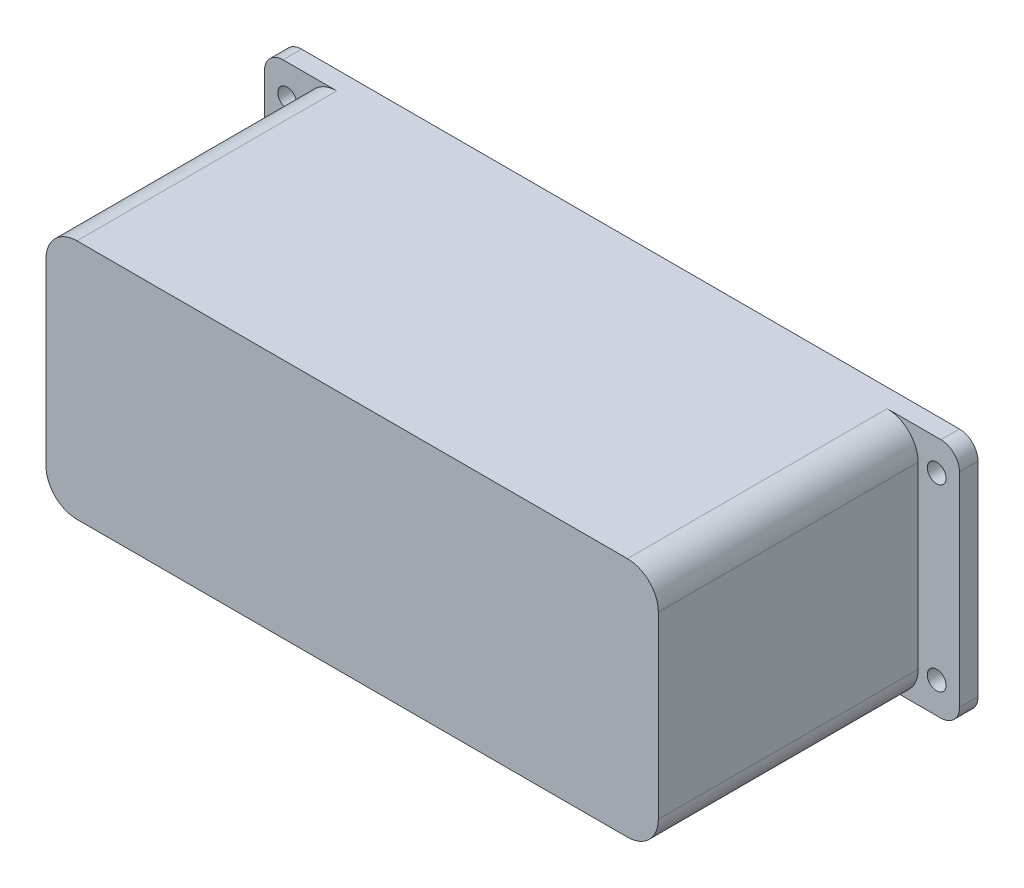
SolidWorks part; units mm, degrees
material "ABS"
ref_plane "前视基准面" through (0, 0, 0) normal (0, 0, 1) x (1, 0, 0)
ref_plane "上视基准面" through (0, 0, 0) normal (0, 1, 0) x (1, 0, 0)
ref_plane "右视基准面" through (0, 0, 0) normal (1, 0, 0) x (0, 0, -1)
other "Configuration Table"
sketch "草图1" plane through (0, 0, 0) normal (0, 0, 1) x (1, 0, 0)
  line L1 (-79.5, -19.5) -> (79.5, -19.5)
  line L2 (-79.5, -19.5) -> (-79.5, 19.5)
  line L3 (-79.5, 19.5) -> (79.5, 19.5)
  line L4 (79.5, -19.5) -> (79.5, 19.5)
  line L5 (-79.5, -19.5) -> (79.5, 19.5) construction
  line L6 (-79.5, 19.5) -> (79.5, -19.5) construction
  point P0 (0, 0)
  dimension "D1" = 159
  dimension "D2" = 39
extrude "凸台-拉伸1" add sketch "草图1" along normal blind 2
fillet "圆角1" radius 3 4 edges at (-79.5, -19.5, 1) (-79.5, 19.5, 1) (79.5, -19.5, 1) (79.5, 19.5, 1)
sketch "草图2" plane through (0, 0, 2) normal (0, 0, 1) x (1, 0, 0)
  line L0 (79.5, -16.5) -> (79.5, 16.5) construction
  line L1 (73, -7.5) -> (86, -7.5)
  line L2 (73, -7.5) -> (73, 7.5)
  line L3 (73, 7.5) -> (86, 7.5)
  line L4 (86, -7.5) -> (86, 7.5)
  line L5 (73, -7.5) -> (86, 7.5) construction
  line L6 (73, 7.5) -> (86, -7.5) construction
  line L8 (-52.5, -14.5) -> (52.5, -14.5) construction
  line L9 (-52.5, -14.5) -> (-52.5, 14.5) construction
  line L10 (-52.5, 14.5) -> (52.5, 14.5) construction
  line L11 (52.5, -14.5) -> (52.5, 14.5) construction
  line L12 (-52.5, -14.5) -> (52.5, 14.5) construction
  line L13 (-52.5, 14.5) -> (52.5, -14.5) construction
  circle A0 centre (52.5, 14.5) radius 1.52
  circle A1 centre (-52.5, 14.5) radius 1.52
  circle A2 centre (-52.5, -14.5) radius 1.52
  circle A3 centre (52.5, -14.5) radius 1.52
  point P0 (79.5, 0)
  point P7 (0, 0)
  dimension "D5" = 3.04
  dimension "D1" = 105
  dimension "D2" = 29
  dimension "D3" = 13
  dimension "D4" = 15
extrude "切除-拉伸1" cut sketch "草图2" against normal blind 55
ref_plane "基准面1" through (0, 0, 4) normal (0, 0, 1) x (1, 0, 0)
sketch "草图4" plane through (0, 0, 4) normal (0, 0, 1) x (1, 0, 0)
  line L8 (79.5, -16.5) -> (79.5, -7.5)
  line L9 (79.5, -7.5) -> (73, -7.5)
  line L10 (73, -7.5) -> (73, 7.5)
  line L11 (73, 7.5) -> (79.5, 7.5)
  line L12 (79.5, 7.5) -> (79.5, 16.5)
  line L13 (76.5, 19.5) -> (-76.5, 19.5)
  line L14 (-79.5, 16.5) -> (-79.5, -16.5)
  line L15 (-76.5, -19.5) -> (76.5, -19.5)
  line L16 (79.5, -16.5) -> (79.5, -7.5)
  line L17 (79.5, -7.5) -> (73, -7.5)
  line L18 (73, -7.5) -> (73, 7.5)
  line L19 (73, 7.5) -> (79.5, 7.5)
  line L20 (79.5, 7.5) -> (79.5, 16.5)
  line L21 (76.5, 19.5) -> (-76.5, 19.5)
  line L22 (-79.5, 16.5) -> (-79.5, -16.5)
  line L23 (-76.5, -19.5) -> (76.5, -19.5)
  arc A4 (79.5, 16.5) -> (76.5, 19.5) centre (76.5, 16.5) ccw
  arc A5 (-76.5, 19.5) -> (-79.5, 16.5) centre (-76.5, 16.5) ccw
  arc A6 (-79.5, -16.5) -> (-76.5, -19.5) centre (-76.5, -16.5) ccw
  arc A7 (76.5, -19.5) -> (79.5, -16.5) centre (76.5, -16.5) ccw
  arc A8 (79.5, 16.5) -> (76.5, 19.5) centre (76.5, 16.5) ccw
  arc A9 (-76.5, 19.5) -> (-79.5, 16.5) centre (-76.5, 16.5) ccw
  arc A10 (-79.5, -16.5) -> (-76.5, -19.5) centre (-76.5, -16.5) ccw
  arc A11 (76.5, -19.5) -> (79.5, -16.5) centre (76.5, -16.5) ccw
  dimension "D1" = 0
extrude "凸台-拉伸2" add sketch "草图4" along normal blind 3 separate body
sketch "草图5" plane through (0, 0, 7) normal (0, 0, 1) x (1, 0, 0)
  line L0 (76.5, 19.5) -> (-76.5, 19.5) construction
  line L1 (-49.5, -19.5) -> (49.5, -19.5)
  line L2 (-49.5, -19.5) -> (-49.5, 19.5)
  line L3 (-49.5, 19.5) -> (49.5, 19.5)
  line L4 (49.5, -19.5) -> (49.5, 19.5)
  line L5 (-49.5, -19.5) -> (49.5, 19.5) construction
  line L6 (-49.5, 19.5) -> (49.5, -19.5) construction
  circle A0 centre (52.5, 14.5) radius 1.52 construction
  point P0 (0, 0)
  dimension "D1" = 3
extrude "凸台-拉伸3" add sketch "草图5" along normal blind 44
sketch "草图7" plane through (0, 0, 7) normal (0, 0, 1) x (1, 0, 0)
  circle A0 centre (-52.5, -14.5) radius 1.52 construction
  circle A1 centre (-52.5, 14.5) radius 1.52 construction
  circle A2 centre (52.5, -14.5) radius 1.52 construction
  circle A3 centre (52.5, 14.5) radius 1.52 construction
  circle A4 centre (-52.5, -14.5) radius 1.52
  circle A5 centre (-52.5, 14.5) radius 1.52
  circle A6 centre (52.5, -14.5) radius 1.52
  circle A7 centre (52.5, 14.5) radius 1.52
extrude "切除-拉伸2" cut sketch "草图7" against normal blind 45
fillet "圆角2" radius 5 4 edges at (49.5, 19.5, 29) (-49.5, 19.5, 29) (-49.5, -19.5, 29) (49.5, -19.5, 29)
sketch "草图8" plane through (0, 0, 4) normal (0, 0, -1) x (-1, 0, 0)
  line L8 (-48.18, 14.5) -> (-48.18, -14.5)
  line L9 (44.5, 18.18) -> (-44.5, 18.18)
  line L10 (48.18, -14.5) -> (48.18, 14.5)
  line L11 (-44.5, -18.18) -> (44.5, -18.18)
  line L12 (-48.18, 14.5) -> (-48.18, -14.5)
  line L13 (44.5, 18.18) -> (-44.5, 18.18)
  line L14 (48.18, -14.5) -> (48.18, 14.5)
  line L15 (-44.5, -18.18) -> (44.5, -18.18)
  arc A4 (48.18, 14.5) -> (44.5, 18.18) centre (44.5, 14.5) ccw
  arc A5 (48.18, 14.5) -> (44.5, 18.18) centre (44.5, 14.5) ccw
  arc A6 (44.5, -18.18) -> (48.18, -14.5) centre (44.5, -14.5) ccw
  arc A7 (44.5, -18.18) -> (48.18, -14.5) centre (44.5, -14.5) ccw
  arc A8 (-48.18, -14.5) -> (-44.5, -18.18) centre (-44.5, -14.5) ccw
  arc A9 (-48.18, -14.5) -> (-44.5, -18.18) centre (-44.5, -14.5) ccw
  arc A10 (-44.5, 18.18) -> (-48.18, 14.5) centre (-44.5, 14.5) ccw
  arc A11 (-44.5, 18.18) -> (-48.18, 14.5) centre (-44.5, 14.5) ccw
  dimension "D1" = 1.32
extrude "切除-拉伸4" cut sketch "草图8" against normal blind 43
sketch "草图9" plane through (0, 0, 0) normal (0, 0, -1) x (-1, 0, 0)
  line L0 (-73, -7.5) -> (-73, 7.5) construction
  line L1 (-73, 7.5) -> (-68, 7.5)
  line L2 (-73, 7.5) -> (-73, -7.5)
  line L3 (-73, -7.5) -> (-68, -7.5)
  line L4 (-68, 7.5) -> (-68, -7.5)
  line L5 (-79.5, 7.5) -> (-79.5, 16.5) construction
  line L6 (-79.5, -7.5) -> (-73, -7.5) construction
  dimension "D1" = 11.5
extrude "切除-拉伸5" cut sketch "草图9" against normal blind 6
sketch "草图10" plane through (0, 0, 0) normal (0, 0, -1) x (-1, 0, 0)
  line L1 (-17.5, -23.5) -> (17.5, -23.5) construction
  line L2 (-17.5, -23.5) -> (-17.5, 23.5) construction
  line L3 (-17.5, 23.5) -> (17.5, 23.5) construction
  line L4 (17.5, -23.5) -> (17.5, 23.5) construction
  line L5 (-17.5, -23.5) -> (17.5, 23.5) construction
  line L6 (-17.5, 23.5) -> (17.5, -23.5) construction
  line L7 (-25, -27.5) -> (25, -27.5)
  line L8 (-25, -27.5) -> (-25, 27.5)
  line L9 (-25, 27.5) -> (25, 27.5)
  line L10 (25, -27.5) -> (25, 27.5)
  line L11 (-25, -27.5) -> (25, 27.5) construction
  line L12 (-25, 27.5) -> (25, -27.5) construction
  line L14 (-76.5, 19.5) -> (76.5, 19.5) construction
  circle A0 centre (-17.5, 23.5) radius 2.025
  circle A1 centre (17.5, 23.5) radius 2.025
  circle A2 centre (-17.5, -23.5) radius 2.025
  circle A3 centre (17.5, -23.5) radius 2.025
  point P0 (0, 0)
  point P6 (0, 0)
  dimension "D5" = 4.05
  dimension "D1" = 35
  dimension "D2" = 4
  dimension "D3" = 50
  dimension "D4" = 4
extrude "凸台-拉伸4" add sketch "草图10" against normal up to surface (2 mm away) up to face at (54.02, 14.5, 2)
fillet "圆角3" radius 4 8 edges at (-25, 19.5, 1) (-25, 27.5, 1) (25, 19.5, 1) (25, -19.5, 1) (25, -27.5, 1) (-25, -27.5, 1) (-25, -19.5, 1) (25, 27.5, 1)
sketch "草图11" plane through (0, 0, 51) normal (0, 0, 1) x (1, 0, 0)
  line L4 (44.5, 19.5) -> (-44.5, 19.5)
  line L5 (-49.5, 14.5) -> (-49.5, -14.5)
  line L6 (-44.5, -19.5) -> (44.5, -19.5)
  line L7 (49.5, -14.5) -> (49.5, 14.5)
  line L8 (44.5, 19.5) -> (-44.5, 19.5)
  line L9 (-49.5, 14.5) -> (-49.5, -14.5)
  line L10 (-44.5, -19.5) -> (44.5, -19.5)
  line L11 (49.5, -14.5) -> (49.5, 14.5)
  arc A4 (-44.5, 19.5) -> (-49.5, 14.5) centre (-44.5, 14.5) ccw
  arc A5 (-49.5, -14.5) -> (-44.5, -19.5) centre (-44.5, -14.5) ccw
  arc A6 (44.5, -19.5) -> (49.5, -14.5) centre (44.5, -14.5) ccw
  arc A7 (49.5, 14.5) -> (44.5, 19.5) centre (44.5, 14.5) ccw
  arc A8 (-44.5, 19.5) -> (-49.5, 14.5) centre (-44.5, 14.5) ccw
  arc A9 (-49.5, -14.5) -> (-44.5, -19.5) centre (-44.5, -14.5) ccw
  arc A10 (44.5, -19.5) -> (49.5, -14.5) centre (44.5, -14.5) ccw
  arc A11 (49.5, 14.5) -> (44.5, 19.5) centre (44.5, 14.5) ccw
  dimension "D1" = 0
extrude "切除-拉伸6" cut sketch "草图11" against normal blind 2
sketch "草图12" plane through (0, 0, 7) normal (0, 0, 1) x (1, 0, 0)
  line L0 (-29, 19.5) -> (29, 19.5)
  line L1 (-29, -19.5) -> (29, -19.5)
  line L12 (21, 27.5) -> (-21, 27.5)
  line L13 (-29, 19.5) -> (-76.5, 19.5)
  line L14 (-79.5, 16.5) -> (-79.5, -16.5)
  line L15 (-76.5, -19.5) -> (-29, -19.5)
  line L16 (-21, -27.5) -> (21, -27.5)
  line L17 (29, -19.5) -> (76.5, -19.5)
  line L18 (79.5, -16.5) -> (79.5, -7.5)
  line L19 (79.5, -7.5) -> (68, -7.5)
  line L20 (68, -7.5) -> (68, 7.5)
  line L21 (68, 7.5) -> (79.5, 7.5)
  line L22 (79.5, 7.5) -> (79.5, 16.5)
  line L23 (76.5, 19.5) -> (29, 19.5)
  line L24 (21, 27.5) -> (-21, 27.5)
  line L28 (-21, -27.5) -> (21, -27.5)
  arc A12 (-21, 27.5) -> (-25, 23.5) centre (-21, 23.5) ccw
  arc A13 (-29, 19.5) -> (-25, 23.5) centre (-29, 23.5) ccw
  arc A14 (-76.5, 19.5) -> (-79.5, 16.5) centre (-76.5, 16.5) ccw
  arc A15 (-79.5, -16.5) -> (-76.5, -19.5) centre (-76.5, -16.5) ccw
  arc A16 (-25, -23.5) -> (-29, -19.5) centre (-29, -23.5) ccw
  arc A17 (-25, -23.5) -> (-21, -27.5) centre (-21, -23.5) ccw
  arc A18 (21, -27.5) -> (25, -23.5) centre (21, -23.5) ccw
  arc A19 (29, -19.5) -> (25, -23.5) centre (29, -23.5) ccw
  arc A20 (76.5, -19.5) -> (79.5, -16.5) centre (76.5, -16.5) ccw
  arc A21 (79.5, 16.5) -> (76.5, 19.5) centre (76.5, 16.5) ccw
  arc A22 (25, 23.5) -> (29, 19.5) centre (29, 23.5) ccw
  arc A23 (25, 23.5) -> (21, 27.5) centre (21, 23.5) ccw
  arc A24 (-21, 27.5) -> (-25, 23.5) centre (-21, 23.5) ccw
  arc A25 (-29, 19.5) -> (-25, 23.5) centre (-29, 23.5) ccw
  arc A28 (-25, -23.5) -> (-29, -19.5) centre (-29, -23.5) ccw
  arc A29 (-25, -23.5) -> (-21, -27.5) centre (-21, -23.5) ccw
  arc A30 (21, -27.5) -> (25, -23.5) centre (21, -23.5) ccw
  arc A31 (29, -19.5) -> (25, -23.5) centre (29, -23.5) ccw
  arc A32 (76.5, -19.5) -> (79.5, -16.5) centre (76.5, -16.5) ccw
  arc A34 (25, 23.5) -> (29, 19.5) centre (29, 23.5) ccw
  arc A35 (25, 23.5) -> (21, 27.5) centre (21, 23.5) ccw
  dimension "D1" = 0
extrude "切除-拉伸7" cut sketch "草图12" against normal blind 32 contours A31 L1 A28 A29 L28 A30 | A34 A35 L24 A24 A25 L0
sketch "草图13" plane through (0, 0, 7) normal (0, 0, 1) x (1, 0, 0)
  line L1 (74, -14.5) -> (-74, -14.5) construction
  line L2 (74, -14.5) -> (74, 14.5) construction
  line L3 (74, 14.5) -> (-74, 14.5) construction
  line L4 (-74, -14.5) -> (-74, 14.5) construction
  line L5 (74, -14.5) -> (-74, 14.5) construction
  line L6 (74, 14.5) -> (-74, -14.5) construction
  circle A0 centre (-74, 14.5) radius 2.025
  circle A1 centre (-74, -14.5) radius 2.025
  circle A2 centre (74, -14.5) radius 2.025
  circle A3 centre (74, 14.5) radius 2.025
  point P0 (0, 0)
  point P12 (-56, 16.1934)
  dimension "D2" = 29
  dimension "D3" = 4.05
  dimension "D1" = 148
extrude "切除-拉伸8" cut sketch "草图13" against normal blind 32
sketch "草图14" plane through (0, 0, 7) normal (0, 0, 1) x (1, 0, 0)
  line L0 (49.5, -14.5) -> (49.5, 14.5) construction
  line L1 (73, 7.5) -> (49.5, 7.5)
  line L2 (73, 7.5) -> (73, -7.5)
  line L3 (73, -7.5) -> (49.5, -7.5)
  line L4 (49.5, 7.5) -> (49.5, -7.5)
  point P7 (73, -7.5)
extrude "切除-拉伸9" cut sketch "草图14" against normal blind 3
sketch "草图15" plane through (0, 0, 0) normal (0, 0, -1) x (-1, 0, 0)
  line L0 (-68, -7.5) -> (-68, 7.5) construction
  line L1 (-68, 7.5) -> (-43, 7.5)
  line L2 (-68, 7.5) -> (-68, -7.5)
  line L3 (-68, -7.5) -> (-43, -7.5)
  line L4 (-43, 7.5) -> (-43, -7.5)
  point P5 (-68, -7.5)
  point P8 (-68, -7.4387)
  point P9 (-68, -1.9017)
  dimension "D1" = 25
extrude "切除-拉伸10" cut sketch "草图15" against normal up to surface (7 mm away)
fillet "圆角4" radius 3 2 edges at (79.5, -7.5, 5.5) (79.5, 7.5, 5.5)
fillet "圆角5" radius 3 2 edges at (79.5, -7.5, 1) (79.5, 7.5, 1)
sketch "草图16" plane through (0, 0, 4) normal (0, 0, -1) x (-1, 0, 0)
  line L0 (-76.5, -7.5) -> (-48.18, -7.5) construction
  line L1 (-48.18, 7.5) -> (-56.18, 7.5)
  line L2 (-48.18, 7.5) -> (-48.18, -7.5)
  line L3 (-48.18, -7.5) -> (-56.18, -7.5)
  line L4 (-56.18, 7.5) -> (-56.18, -7.5)
  dimension "D1" = 8
extrude "凸台-拉伸5" add sketch "草图16" against normal up to surface (3 mm away)
sketch "草图17" plane through (0, 0, 7) normal (0, 0, 1) x (1, 0, 0)
  line L0 (-44.5, 19.5) -> (-76.5, 19.5) construction
  line L1 (-56.18, 19.5) -> (-79.5, 19.5)
  line L2 (-56.18, 19.5) -> (-56.18, -19.5)
  line L3 (-56.18, -19.5) -> (-79.5, -19.5)
  line L4 (-79.5, 19.5) -> (-79.5, -19.5)
  line L5 (-76.5, -19.5) -> (-44.5, -19.5) construction
  line L6 (-79.5, 16.5) -> (-79.5, -16.5) construction
  line L7 (0, 0) -> (0, -50000) construction
  line L8 (79.5, 19.5) -> (79.5, -19.5)
  line L9 (56.18, -19.5) -> (79.5, -19.5)
  line L10 (56.18, 19.5) -> (56.18, -19.5)
  line L11 (56.18, 19.5) -> (79.5, 19.5)
  line L12 (56.18, 7.5) -> (56.18, -7.5) construction
extrude "切除-拉伸11" cut sketch "草图17" against normal up to surface (5 mm away)
fillet "圆角6" radius 3 4 edges at (56.18, -19.5, 5.5) (56.18, 19.5, 5.5) (-56.18, 19.5, 5.5) (-56.18, -19.5, 5.5)
sketch "草图18" plane through (0, 0, 0) normal (0, 0, -1) x (-1, 0, 0)
  line L8 (-43, -7.5) -> (-76.5, -7.5)
  line L9 (-79.5, -10.5) -> (-79.5, -16.5)
  line L10 (-76.5, -19.5) -> (76.5, -19.5)
  line L11 (79.5, -16.5) -> (79.5, 16.5)
  line L12 (76.5, 19.5) -> (-76.5, 19.5)
  line L13 (-79.5, 16.5) -> (-79.5, 10.5)
  line L14 (-76.5, 7.5) -> (-43, 7.5)
  line L15 (-43, 7.5) -> (-43, -7.5)
  line L16 (-43, -7.5) -> (-76.5, -7.5)
  line L17 (-79.5, -10.5) -> (-79.5, -16.5)
  line L18 (-76.5, -19.5) -> (76.5, -19.5)
  line L19 (79.5, -16.5) -> (79.5, 16.5)
  line L20 (76.5, 19.5) -> (-76.5, 19.5)
  line L21 (-79.5, 16.5) -> (-79.5, 10.5)
  line L22 (-76.5, 7.5) -> (-43, 7.5)
  line L23 (-43, 7.5) -> (-43, -7.5)
  arc A6 (-76.5, -7.5) -> (-79.5, -10.5) centre (-76.5, -10.5) ccw
  arc A7 (-79.5, -16.5) -> (-76.5, -19.5) centre (-76.5, -16.5) ccw
  arc A8 (76.5, -19.5) -> (79.5, -16.5) centre (76.5, -16.5) ccw
  arc A9 (79.5, 16.5) -> (76.5, 19.5) centre (76.5, 16.5) ccw
  arc A10 (-76.5, 19.5) -> (-79.5, 16.5) centre (-76.5, 16.5) ccw
  arc A11 (-79.5, 10.5) -> (-76.5, 7.5) centre (-76.5, 10.5) ccw
  arc A12 (-76.5, -7.5) -> (-79.5, -10.5) centre (-76.5, -10.5) ccw
  arc A13 (-79.5, -16.5) -> (-76.5, -19.5) centre (-76.5, -16.5) ccw
  arc A14 (76.5, -19.5) -> (79.5, -16.5) centre (76.5, -16.5) ccw
  arc A15 (79.5, 16.5) -> (76.5, 19.5) centre (76.5, 16.5) ccw
  arc A16 (-76.5, 19.5) -> (-79.5, 16.5) centre (-76.5, 16.5) ccw
  arc A17 (-79.5, 10.5) -> (-76.5, 7.5) centre (-76.5, 10.5) ccw
  dimension "D1" = 0
extrude "切除-拉伸12" cut sketch "草图18" against normal up to surface (2 mm away)
